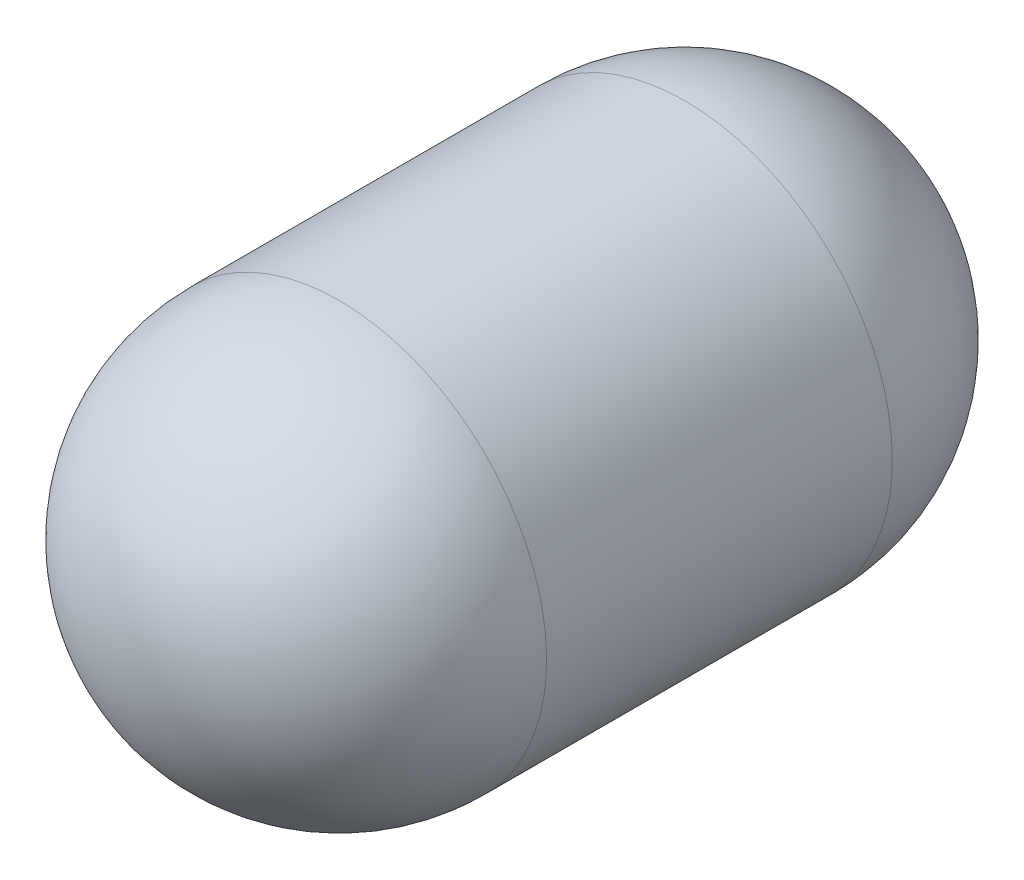
SolidWorks part; units mm, degrees
material "Custom Plastic (2)"
ref_plane "Front Plane" through (0, 0, 0) normal (0, 0, 1) x (1, 0, 0)
ref_plane "Top Plane" through (0, 0, 0) normal (0, 1, 0) x (1, 0, 0)
ref_plane "Right Plane" through (0, 0, 0) normal (1, 0, 0) x (0, 0, -1)
sketch "Tank Arc" plane through (0, 0, 0) normal (1, 0, 0) x (0, 0, -1)
  line L0 (-63.5, 76.2) -> (63.5, 76.2)
  line L1 (0, 0) -> (0, 76.2) construction
  line L3 (139.7, 0) -> (-139.7, 0)
  arc A0 (63.5, 76.2) -> (139.7, 0) centre (63.5, 0) cw
  arc A1 (-63.5, 76.2) -> (-139.7, 0) centre (-63.5, 0) ccw
  dimension "D1" = 76.2
  dimension "D2" = 279.4
revolve "Air Tank" add sketch "Tank Arc" angle 360 about L3
